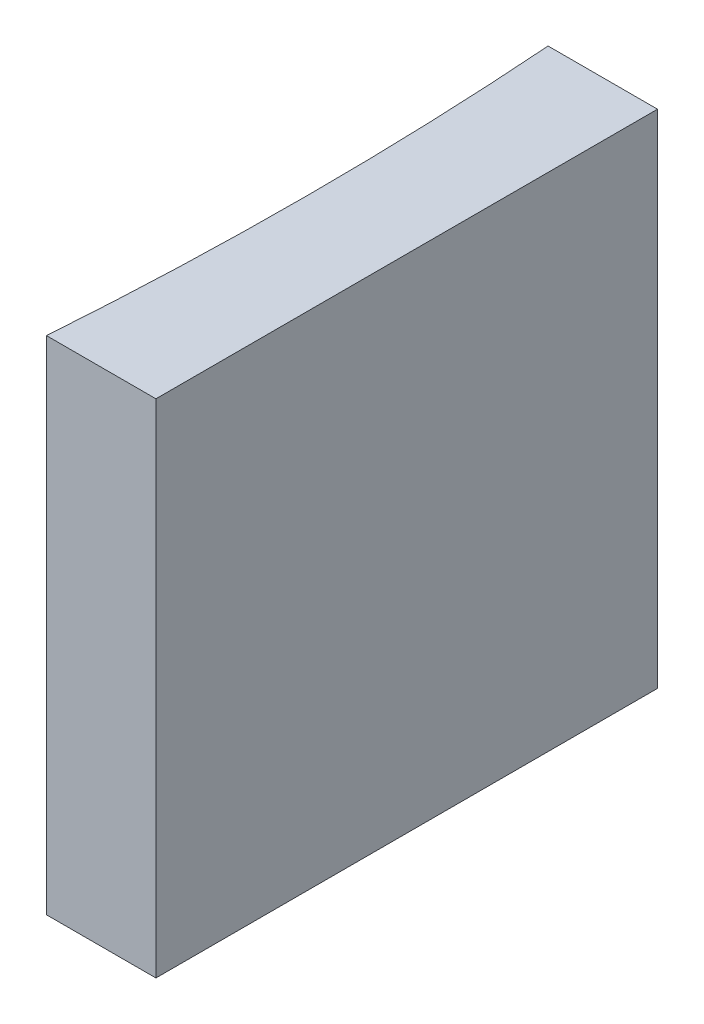
SolidWorks part; units mm, degrees
ref_plane "前视基准面" through (0, 0, 0) normal (0, 0, 1) x (1, 0, 0)
ref_plane "上视基准面" through (0, 0, 0) normal (0, 1, 0) x (1, 0, 0)
ref_plane "右视基准面" through (0, 0, 0) normal (1, 0, 0) x (0, 0, -1)
sketch "草图1" plane through (0, 0, 0) normal (0, 1, 0) x (1, 0, 0)
  line L0 (0, 0) -> (0, -10)
  line L1 (0, 0) -> (-2.182, 0)
  line L2 (0, -10) -> (-2.182, -10)
  line L3 (21.2259, -5) -> (-21.2259, -5) construction
  arc A0 (-2.182, -10) -> (-2.182, 0) centre (-70.78, -5) ccw
  point P7 (-2, -5)
  point P8 (0, -5)
  dimension "D2" = 68.78
  dimension "D3" = 2
  dimension "D1" = 10
extrude "凸台-拉伸1" add sketch "草图1" along normal blind 10
